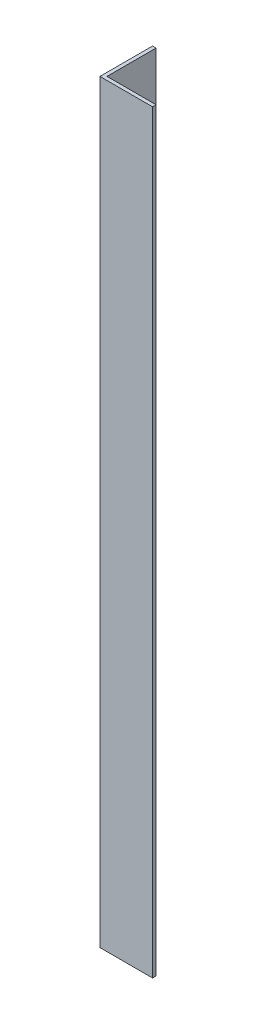
SolidWorks part; units mm, degrees
material "1060 Сплав"
ref_plane "Спереди" through (0, 0, 0) normal (0, 0, 1) x (1, 0, 0)
ref_plane "Сверху" through (0, 0, 0) normal (0, 1, 0) x (1, 0, 0)
ref_plane "Справа" through (0, 0, 0) normal (1, 0, 0) x (0, 0, -1)
sketch "Эскиз1" plane through (0, 0, 0) normal (0, 1, 0) x (1, 0, 0)
  line L0 (0, 0) -> (0, 15)
  line L1 (0, 15) -> (1, 15)
  line L2 (1, 15) -> (1, 1)
  line L3 (1, 1) -> (15, 1)
  line L4 (15, 1) -> (15, 0)
  line L5 (15, 0) -> (0, 0)
  dimension "D1" = 1
  dimension "D2" = 15
extrude "Бобышка-Вытянуть1" add sketch "Эскиз1" along normal blind 215
